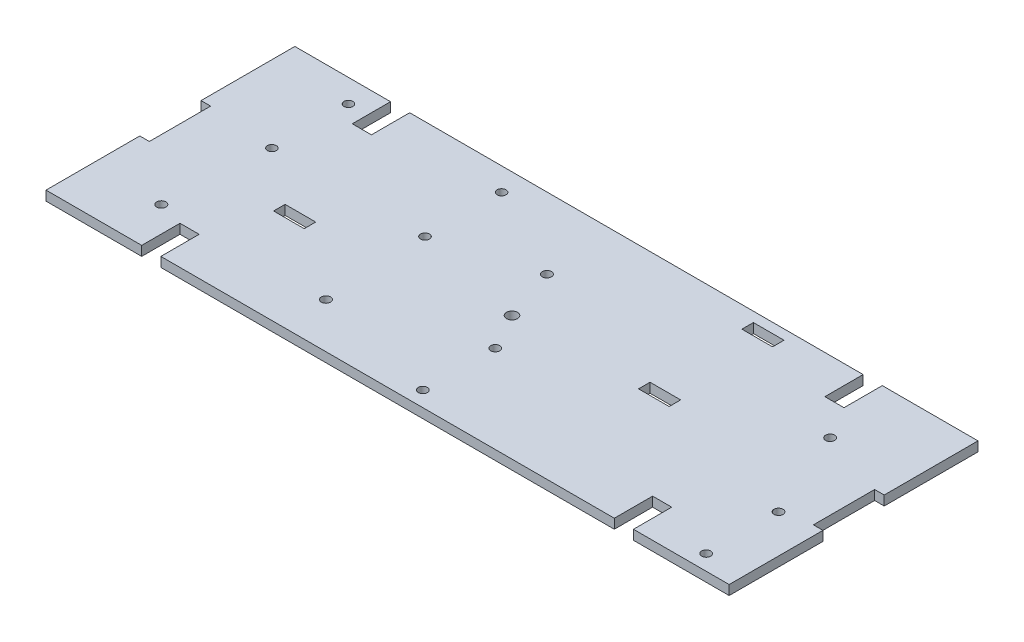
SolidWorks part; units mm, degrees
material "S-Glass Fiber"
ref_plane "Front Plane" through (0, 0, 0) normal (0, 0, 1) x (1, 0, 0)
ref_plane "Top Plane" through (0, 0, 0) normal (0, 1, 0) x (1, 0, 0)
ref_plane "Right Plane" through (0, 0, 0) normal (1, 0, 0) x (0, 0, -1)
sketch "Sketch1" plane through (0, 0, 0) normal (0, 1, 0) x (1, 0, 0)
  line L0 (-226.6315, 82.55) -> (-194.8815, 82.55)
  line L9 (-194.8815, 82.55) -> (-194.8815, 69.85)
  line L10 (-194.8815, 69.85) -> (-188.5315, 69.85)
  line L11 (-188.5315, 69.85) -> (-188.5315, 82.55)
  line L12 (-188.5315, 82.55) -> (-38.1, 82.55)
  line L13 (-38.1, 82.55) -> (-38.1, 69.85)
  line L14 (-38.1, 69.85) -> (-31.75, 69.85)
  line L15 (-31.75, 69.85) -> (-31.75, 82.55)
  line L16 (-31.75, 82.55) -> (0, 82.55)
  line L17 (0, 82.55) -> (0, 51.435)
  line L21 (0, 31.115) -> (0, 0)
  line L22 (0, 0) -> (-31.75, 0)
  line L23 (-31.75, 0) -> (-31.75, 12.7)
  line L24 (-31.75, 12.7) -> (-38.1, 12.7)
  line L25 (-38.1, 12.7) -> (-38.1, 0)
  line L26 (-38.1, 0) -> (-188.5315, 0)
  line L27 (-188.5315, 0) -> (-188.5315, 12.7)
  line L28 (-188.5315, 12.7) -> (-194.8815, 12.7)
  line L29 (-194.8815, 12.7) -> (-194.8815, 0)
  line L30 (-194.8815, 0) -> (-226.6315, 0)
  line L31 (-226.6315, 0) -> (-226.6315, 31.115)
  line L35 (-226.6315, 51.435) -> (-226.6315, 82.55)
  line L36 (-223.4565, 41.275) -> (-3.175, 41.275) construction
  line L37 (-226.6315, 51.435) -> (-223.4565, 51.435)
  line L39 (-226.6315, 31.115) -> (-223.4565, 31.115)
  line L40 (-223.4565, 51.435) -> (-223.4565, 31.115)
  line L41 (0, 51.435) -> (-3.175, 51.435)
  line L43 (0, 31.115) -> (-3.175, 31.115)
  line L44 (-3.175, 51.435) -> (-3.175, 31.115)
  line L45 (-113.3157, 82.55) -> (-113.3157, 0) construction
  circle A2 centre (-113.3158, 41.275) radius 1.8288
  dimension "D9" = 3.6576
  dimension "D1" = 82.55
  dimension "D2" = 226.6315
  dimension "D3" = 3.175
  dimension "D4" = 6.35
  dimension "D5" = 12.7
  dimension "D6" = 20.32
  dimension "D7" = 31.75
  dimension "D8" = 3.175
extrude "Boss-Extrude1" add sketch "Sketch1" along normal blind 3.175
sketch "Sketch3" plane through (0, 3.175, 0) normal (0, 1, 0) x (1, 0, 0)
  line L0 (-31.75, 0) -> (0, 0) construction
  line L1 (0, 0) -> (0, 31.115) construction
  circle A0 centre (-106.7, 29.08) radius 1.5
  circle A1 centre (-106.7, 5.08) radius 1.5
  circle A2 centre (-12.7, 5.08) radius 1.5
  circle A3 centre (-12.7, 29.08) radius 1.5
  dimension "D1" = 3
  dimension "D2" = 94
  dimension "D3" = 24
  dimension "D4" = 5.08
  dimension "D5" = 12.7
extrude "Cut-Extrude1" cut sketch "Sketch3" against normal through all
sketch "Sketch4" plane through (0, 3.175, 0) normal (0, 1, 0) x (1, 0, 0)
  line L0 (-226.6315, 82.55) -> (-226.6315, 51.435) construction
  line L1 (-194.8815, 82.55) -> (-226.6315, 82.55) construction
  circle A0 centre (-150.4315, 49.53) radius 1.4732
  circle A1 centre (-150.4315, 74.93) radius 1.4732
  circle A2 centre (-201.2315, 74.93) radius 1.4732
  circle A3 centre (-201.2315, 49.53) radius 1.4732
  dimension "D1" = 2.9464
  dimension "D2" = 50.8
  dimension "D3" = 25.4
  dimension "D4" = 25.4
  dimension "D5" = 7.62
extrude "Cut-Extrude2" cut sketch "Sketch4" against normal through all
sketch "Sketch5" plane through (0, 3.175, 0) normal (0, 1, 0) x (1, 0, 0)
  line L0 (-226.6315, 14.9968) -> (-148.7596, 14.9968) construction
  line L1 (-226.6315, 31.115) -> (-226.6315, 0) construction
  line L2 (-177.7976, 0) -> (-177.7976, 31.75) construction
  line L3 (-188.5315, 0) -> (-38.1, 0) construction
  line L4 (0, 58.9138) -> (-119.38, 58.9138) construction
  line L5 (-182.8776, 35.56) -> (-172.7176, 35.56)
  line L6 (-182.8776, 35.56) -> (-182.8776, 31.75)
  line L7 (-182.8776, 31.75) -> (-172.7176, 31.75)
  line L8 (-172.7176, 35.56) -> (-172.7176, 31.75)
  line L9 (0, 51.435) -> (0, 82.55) construction
  line L10 (-71.2448, 82.55) -> (-71.2448, 44.9947) construction
  line L11 (-38.1, 82.55) -> (-188.5315, 82.55) construction
  line L13 (-71.2448, 44.9947) -> (-61.0848, 44.9947)
  line L14 (-71.2448, 44.9947) -> (-71.2448, 41.1847)
  line L15 (-71.2448, 41.1847) -> (-61.0848, 41.1847)
  line L16 (-61.0848, 44.9947) -> (-61.0848, 41.1847)
  line L17 (-71.2448, 79.2847) -> (-61.0848, 79.2847)
  line L18 (-71.2448, 79.2847) -> (-71.2448, 75.4747)
  line L19 (-71.2448, 75.4747) -> (-61.0848, 75.4747)
  line L20 (-61.0848, 79.2847) -> (-61.0848, 75.4747)
  circle A0 centre (-203.3696, 14.9968) radius 1.524
  circle A1 centre (-148.7596, 14.9968) radius 1.524
  circle A2 centre (-25.4, 58.9138) radius 1.524
  circle A3 centre (-119.38, 58.9138) radius 1.524
  dimension "D5" = 3.048
  dimension "D1" = 3.81
  dimension "D2" = 10.16
  dimension "D3" = 31.75
  dimension "D4" = 54.61
  dimension "D6" = 25.4
  dimension "D7" = 93.98
  dimension "D8" = 30.48
extrude "Cut-Extrude3" cut sketch "Sketch5" against normal through all
